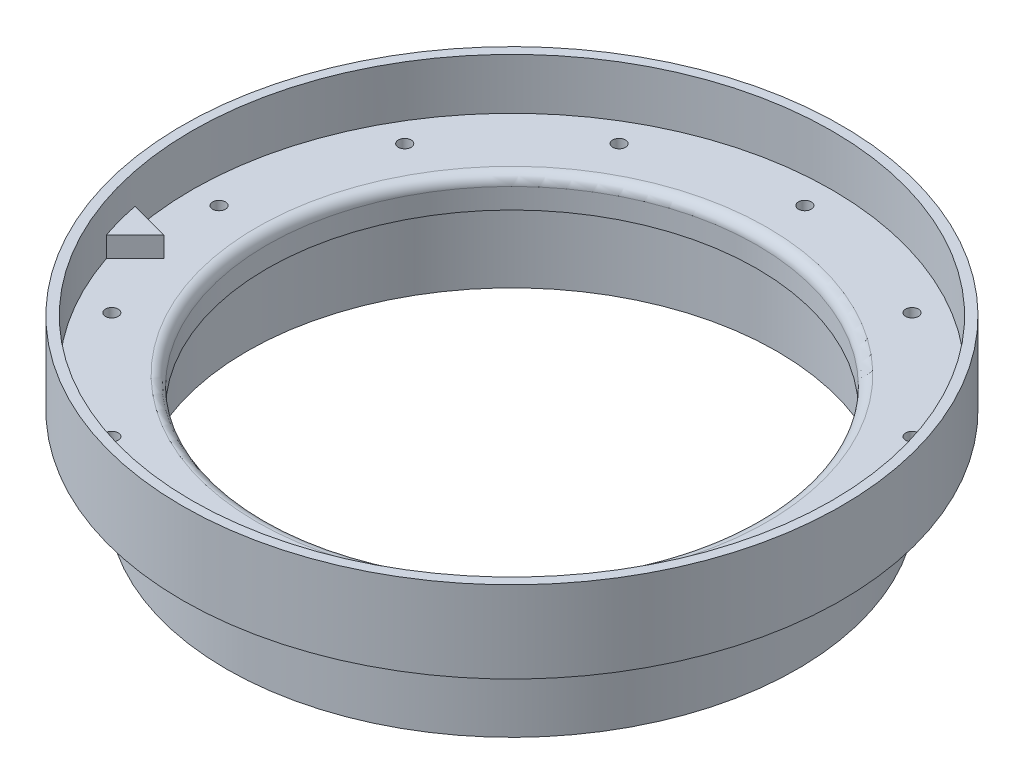
SolidWorks part; units mm, degrees
material "6061-T6 (SS)"
ref_plane "Front Plane" through (0, 0, 0) normal (0, 0, 1) x (1, 0, 0)
ref_plane "Top Plane" through (0, 0, 0) normal (0, 1, 0) x (1, 0, 0)
ref_plane "Right Plane" through (0, 0, 0) normal (1, 0, 0) x (0, 0, -1)
ref_axis "Axis1" through (0, 55, 0) along (0, -1, 0)
sketch "Cross Section" plane through (0, 0, 0) normal (0, 0, 1) x (1, 0, 0)
  line L0 (-38.1, 0) -> (-38.1, -3.175)
  line L1 (-38.1, -3.175) -> (-41.2242, -3.175)
  line L2 (-41.2242, -3.175) -> (-41.2242, -15.875)
  line L4 (0, -15.875) -> (-38.1, -15.875) construction
  line L5 (-44.3992, -15.875) -> (-44.3992, -3.175)
  line L6 (-44.3992, -3.175) -> (-51.2572, -3.175)
  line L7 (-51.2572, -3.175) -> (-51.2572, 9.525)
  line L8 (-51.2572, 9.525) -> (-49.784, 9.525)
  line L9 (-49.784, 9.525) -> (-49.784, 1.5875)
  line L11 (-38.1, 0) -> (0, 0) construction
  line L13 (-44.3992, -15.875) -> (-41.2242, -15.875)
  line L14 (-49.784, 1.5875) -> (-49.784, 3.175) construction
  line L15 (-39.6875, 1.5875) -> (-49.784, 1.5875)
  arc A0 (-39.6875, 1.5875) -> (-38.1, 0) centre (-39.6875, 0) cw
  dimension "D2" = 1.5875
  dimension "D1" = 3.1242
  dimension "D3" = 3.175
  dimension "D5" = 6.858
  dimension "D6" = 12.7
  dimension "D9" = 3.175
  dimension "D4" = 1.5875
  dimension "D7" = 38.1
revolve "Main" add sketch "Cross Section" angle 360 about axis through (0, 55, 0) along (0, -1, 0)
sketch "Hole Location" plane through (0, 0, 0) normal (0, 1, 0) x (1, 0, 0)
  line L0 (0, 0) -> (-45.5549, 0) construction
  circle A0 centre (0, 0) radius 45.5549 construction
  dimension "D1" = 91.1098
hole_wizard "#3-48 Tapped Hole1" positions "Sketch1" profile "Sketch2" tap size "#3-48" standard "ANSI Inch" end condition through all
sketch "Sketch1" plane through (0, 1.5875, 0) normal (0, 1, 0) x (1, 0, 0)
  point P0 (-45.5549, 0)
sketch "Sketch2" plane through (-45.5549, 1.5875, 0) normal (1, 0, 0) x (0, 0, 1)
  line L0 (0, 0) -> (0, 17.4625)
  line L1 (0, 17.4625) -> (0.9969, 17.4625)
  line L2 (0.9969, 17.4625) -> (0.9969, 0)
  line L5 (0.9969, 0) -> (0, 0)
  line L11 (0, -6.35) -> (0, 107.95) construction
  dimension "Thru Tap Drill Dia." = 1.9939
  dimension "Thru Tap Drill Depth" = 17.4625
cosmetic thread "Hole Thread1" parameters "D2"=2.5146
pattern_circular "CirPattern1" count 12 over 360 about axis through (0, 0, 0) along (0, 1, 0) of "#3-48 Tapped Hole1"
sketch "Sketch3" plane through (0, 1.5875, 0) normal (0, 1, 0) x (1, 0, 0)
  line L0 (0, 0) -> (-48.0877, -12.885) construction
  line L1 (0, 0) -> (-45.5549, 0) construction
  line L2 (-47.168, -15.9256) -> (-42.6779, -11.4355)
  line L3 (-42.6779, -11.4355) -> (-48.8115, -9.792)
  circle A0 centre (0, 0) radius 49.784 construction
  circle A1 centre (0, 0) radius 49.784 construction
  arc A2 (-47.168, -15.9256) -> (-48.8115, -9.792) centre (0, 0) cw
  dimension "D1" = 15
  dimension "D2" = 60
  dimension "D3" = 6.35
extrude "Boss-Extrude1" add sketch "Sketch3" along normal blind 3.175
equation "\"D1@Hole Location\"=\"TANK DIAMETER@Cryo Tank.Assembly\"+\"GASKET SEAT THICKNESS@Cryo Tank.Assembly\"+\"LINER THICKNESS@Cryo Tank.Assembly\"+\"SHRINK FIT DELTA@Cryo Tank.Assembly\""
equation "\"D1@Cross Section\"=\"LINER THICKNESS@Cryo Tank.Assembly\"-0.002"
equation "\"D3@Cross Section\"=\"ALUMINUM LAP THICKNESS@Cryo Tank.Assembly\""
equation "\"D5@Cross Section\"=2*\"CF THICKNESS@Cryo Tank.Assembly\"+\"NOMEX THICKNESS@Cryo Tank.Assembly\""
equation "\"D7@Cross Section\"=\"TANK DIAMETER@Cryo Tank.Assembly\"/2"
